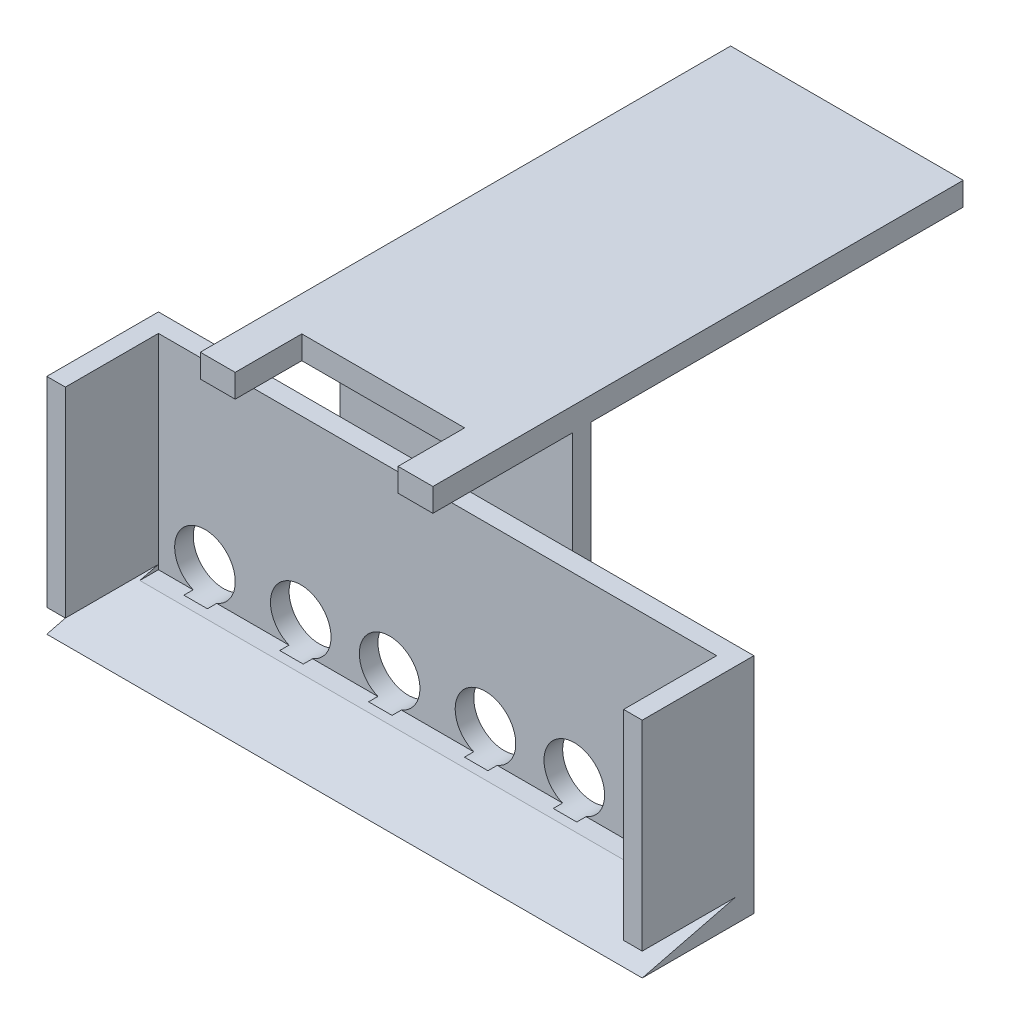
SolidWorks part; units mm, degrees
material "ABS"
ref_plane "Front Plane" through (0, 0, 0) normal (0, 0, 1) x (1, 0, 0)
ref_plane "Top Plane" through (0, 0, 0) normal (0, 1, 0) x (1, 0, 0)
ref_plane "Right Plane" through (0, 0, 0) normal (1, 0, 0) x (0, 0, -1)
sketch "Sketch1" plane through (0, 0, 0) normal (0, 1, 0) x (1, 0, 0)
  line L1 (-76.2, -12.7) -> (76.2, -12.7)
  line L2 (-76.2, -12.7) -> (-76.2, 12.7)
  line L3 (-76.2, 12.7) -> (76.2, 12.7)
  line L4 (76.2, -12.7) -> (76.2, 12.7)
  line L5 (-76.2, -12.7) -> (76.2, 12.7) construction
  line L6 (-76.2, 12.7) -> (76.2, -12.7) construction
  point P0 (0, 0)
  dimension "D1" = 152.4
extrude "Boss-Extrude1" add sketch "Sketch1" along normal blind 5.08 contours L3 L4 L1 L2
ref_plane "Plane1" through (0, 0, 0) normal (1, 0, 0) x (0, 0, -1)
ref_plane "Plane2" through (76.2, 0, 0) normal (1, 0, 0) x (0, 0, -1)
sketch "Sketch4" plane through (76.2, 0, 0) normal (1, 0, 0) x (0, 0, -1)
  line L0 (-12.7, 0) -> (-12.7, 5.08)
  line L1 (-12.7, 5.08) -> (-12.7, 60.96)
  line L2 (-12.7, 60.96) -> (12.7, 60.96)
  line L3 (12.7, 60.96) -> (12.7, 5.08)
  line L4 (12.7, 5.08) -> (12.7, 0)
  line L5 (12.7, 0) -> (-12.7, 0)
extrude "Boss-Extrude2" add sketch "Sketch4" along normal blind 5.08
mirror "Mirror1" about plane through (0, 0, 0) normal (1, 0, 0) of "Boss-Extrude2"
sketch "Sketch5" plane through (0, 0, -12.7) normal (0, 0, -1) x (-1, 0, 0)
  line L1 (-81.28, 60.96) -> (81.28, 60.96)
  line L2 (-81.28, 60.96) -> (-81.28, 0)
  line L3 (-81.28, 0) -> (81.28, 0)
  line L4 (81.28, 60.96) -> (81.28, 0)
extrude "Boss-Extrude3" add sketch "Sketch5" along normal blind 5.08
sketch "Sketch6" plane through (81.28, 0, 0) normal (1, 0, 0) x (0, 0, -1)
  line L0 (-12.7, 0) -> (12.7, 6.35)
  line L1 (-12.7, 0) -> (-12.7, 6.35)
  line L10 (-12.7, 60.96) -> (-12.7, 0) construction
  line L11 (-12.7, 6.35) -> (12.7, 6.35)
  line L12 (17.78, 60.96) -> (17.78, 0) construction
  dimension "D1" = 5.08
extrude "Cut-Extrude2" cut sketch "Sketch6" against normal through all contours L0 L11 L1
sketch "Sketch7" plane through (0, 0, -17.78) normal (0, 0, -1) x (-1, 0, 0)
  line L0 (-31.75, 50.8) -> (31.75, 50.8)
  line L1 (-81.28, 0) -> (81.28, 0) construction
  line L2 (-31.75, 50.8) -> (-31.75, 88.9)
  line L3 (-31.75, 88.9) -> (31.75, 88.9)
  line L4 (31.75, 88.9) -> (31.75, 50.8)
  point P3 (0, 50.8)
  dimension "D1" = 50.8
  dimension "D2" = 38.1
extrude "Boss-Extrude4" add sketch "Sketch7" along normal blind 5.08 contours L2 L3 L4 L0
sketch "Sketch8" plane through (0, 88.9, 0) normal (0, 1, 0) x (1, 0, 0)
  line L0 (-31.75, 22.86) -> (-31.75, 124.46)
  line L1 (-31.75, 22.86) -> (-31.75, 17.78)
  line L2 (-31.75, 17.78) -> (-31.75, -20.32)
  line L3 (-31.75, -20.32) -> (31.75, -20.32)
  line L4 (31.75, -20.32) -> (31.75, 17.78)
  line L5 (31.75, 17.78) -> (31.75, 22.86)
  line L6 (31.75, 22.86) -> (31.75, 124.46)
  line L7 (31.75, 124.46) -> (-31.75, 124.46)
  dimension "D1" = 101.6
extrude "Boss-Extrude5" add sketch "Sketch8" along normal blind 6.35
sketch "Sketch9" plane through (0, 95.25, 0) normal (0, 1, 0) x (1, 0, 0)
  line L1 (22.225, -41.1636) -> (-22.225, -41.1636)
  line L2 (22.225, -41.1636) -> (22.225, -2.13)
  line L3 (22.225, -2.13) -> (-22.225, -2.13)
  line L4 (-22.225, -41.1636) -> (-22.225, -2.13)
  point P0 (0, 0)
extrude "Cut-Extrude3" cut sketch "Sketch9" against normal up to next contours L3 L4 L1 L2
sketch "Sketch10" plane through (0, 0, -12.7) normal (0, 0, 1) x (1, 0, 0)
  line L0 (-13.081, 12.7) -> (13.081, 12.7) construction
  line L1 (-81.28, 0) -> (81.28, 0) construction
  line L2 (-76.2, 6.35) -> (-76.2, 60.96) construction
  line L3 (76.2, 6.35) -> (76.2, 60.96) construction
  line L4 (37.338, 12.7) -> (63.5, 12.7) construction
  line L5 (-13.081, 12.7) -> (13.081, 12.7) construction
  line L7 (-63.5, 12.7) -> (-37.338, 12.7) construction
  circle A0 centre (-13.081, 12.7) radius 8.2697
  circle A1 centre (13.081, 12.7) radius 8.2697
  circle A6 centre (37.338, 12.7) radius 8.2697
  circle A7 centre (63.5, 12.7) radius 8.2697
  circle A10 centre (-63.5, 12.7) radius 8.2697
  circle A11 centre (-37.338, 12.7) radius 8.2697
  arc A12 (-12.0015, 4.5011) -> (-4.8113, 12.7) centre (-13.081, 12.7) ccw [skipped]
  arc A13 (4.8113, 12.7) -> (14.1605, 4.5011) centre (13.081, 12.7) ccw [skipped]
  point P3 (0, 12.7)
  dimension "D2" = 76.2
  dimension "D5" = 26.162
  dimension "D1" = 12.7
  dimension "D4" = 2
  dimension "D6" = 26.162
  dimension "D7" = 12.7
  dimension "D8" = 12.7
  dimension "D3" = 2
extrude "Cut-Extrude4" cut sketch "Sketch10" against normal through all and the other way blind 2.54
